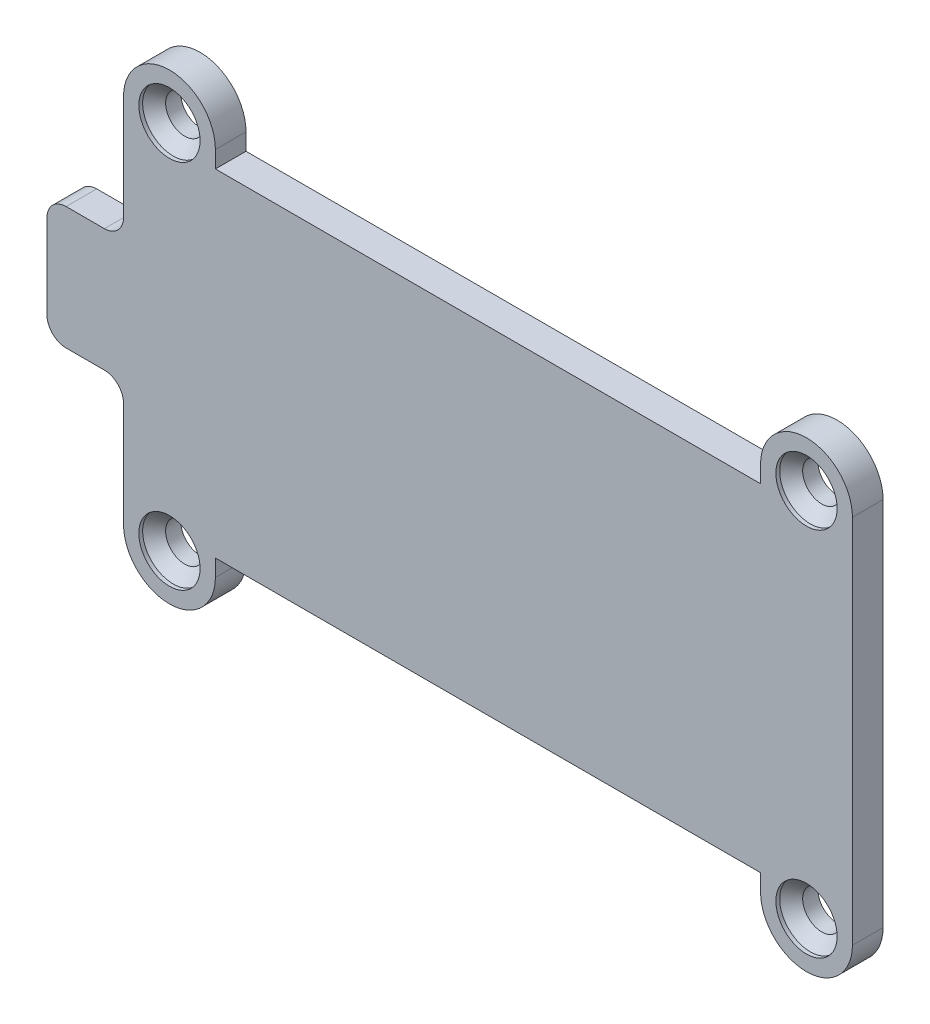
SolidWorks part; units mm, degrees
ref_plane "Front Plane" through (0, 0, 0) normal (0, 0, 1) x (1, 0, 0)
ref_plane "Top Plane" through (0, 0, 0) normal (0, 1, 0) x (1, 0, 0)
ref_plane "Right Plane" through (0, 0, 0) normal (1, 0, 0) x (0, 0, -1)
sketch "Sketch1" plane through (0, 0, 0) normal (0, 0, 1) x (1, 0, 0)
  line L3 (-28.8, 2.25) -> (-28.8, -2.25)
  line L4 (23.8, 12.1) -> (23.8, -12.1)
  line L52 (-25.05, 4) -> (-27.55, 4)
  line L53 (-28.8, 2.75) -> (-28.8, 2.25)
  line L54 (-28.8, 2.25) -> (-21.9, 2.25)
  line L55 (-21.9, 2.25) -> (-21.9, 9.1)
  line L56 (-21.9, 9.1) -> (21.9, 9.1)
  line L57 (21.9, 9.1) -> (21.9, 3.8)
  line L58 (21.9, 3.8) -> (23.8, 3.8)
  line L59 (23.8, 3.8) -> (23.8, 12.1)
  line L60 (17.8, 12.1) -> (17.8, 11)
  line L61 (17.8, 11) -> (-17.8, 11)
  line L62 (-17.8, 11) -> (-17.8, 12.1)
  line L63 (-23.8, 12.1) -> (-23.8, 5.25)
  line L64 (-25.05, 4) -> (-27.55, 4)
  line L65 (-28.8, 2.75) -> (-28.8, 2.25)
  line L72 (17.8, 12.1) -> (17.8, 11)
  line L73 (17.8, 11) -> (-17.8, 11)
  line L74 (-17.8, 11) -> (-17.8, 12.1)
  line L75 (-23.8, 12.1) -> (-23.8, 5.25)
  line L76 (-28.8, -2.25) -> (-28.8, -2.75)
  line L77 (-27.55, -4) -> (-25.05, -4)
  line L78 (-23.8, -5.25) -> (-23.8, -12.1)
  line L79 (-17.8, -12.1) -> (-17.8, -11)
  line L80 (-17.8, -11) -> (17.8, -11)
  line L81 (17.8, -11) -> (17.8, -12.1)
  line L82 (23.8, -12.1) -> (23.8, -3.8)
  line L83 (23.8, -3.8) -> (21.9, -3.8)
  line L84 (21.9, -3.8) -> (21.9, -9.1)
  line L85 (21.9, -9.1) -> (-21.9, -9.1)
  line L86 (-21.9, -9.1) -> (-21.9, -2.25)
  line L87 (-21.9, -2.25) -> (-28.8, -2.25)
  line L88 (-28.8, -2.25) -> (-28.8, -2.75)
  line L89 (-27.55, -4) -> (-25.05, -4)
  line L90 (-23.8, -5.25) -> (-23.8, -12.1)
  line L91 (-17.8, -12.1) -> (-17.8, -11)
  line L92 (-17.8, -11) -> (17.8, -11)
  line L93 (17.8, -11) -> (17.8, -12.1)
  circle A20 centre (-20.8, 12.1) radius 1.25
  circle A21 centre (20.8, 12.1) radius 1.25
  circle A22 centre (20.8, -12.1) radius 1.25
  circle A23 centre (-20.8, -12.1) radius 1.25
  arc A24 (-27.55, 4) -> (-28.8, 2.75) centre (-27.55, 2.75) ccw
  arc A25 (23.8, 12.1) -> (17.8, 12.1) centre (20.8, 12.1) ccw
  arc A26 (-17.8, 12.1) -> (-23.8, 12.1) centre (-20.8, 12.1) ccw
  arc A27 (-25.05, 4) -> (-23.8, 5.25) centre (-25.05, 5.25) ccw
  arc A28 (-27.55, 4) -> (-28.8, 2.75) centre (-27.55, 2.75) ccw
  arc A29 (23.8, 12.1) -> (17.8, 12.1) centre (20.8, 12.1) ccw
  arc A30 (-17.8, 12.1) -> (-23.8, 12.1) centre (-20.8, 12.1) ccw
  arc A31 (-25.05, 4) -> (-23.8, 5.25) centre (-25.05, 5.25) ccw
  arc A32 (-28.8, -2.75) -> (-27.55, -4) centre (-27.55, -2.75) ccw
  arc A33 (-23.8, -5.25) -> (-25.05, -4) centre (-25.05, -5.25) ccw
  arc A34 (-23.8, -12.1) -> (-17.8, -12.1) centre (-20.8, -12.1) ccw
  arc A35 (17.8, -12.1) -> (23.8, -12.1) centre (20.8, -12.1) ccw
  arc A36 (-28.8, -2.75) -> (-27.55, -4) centre (-27.55, -2.75) ccw
  arc A37 (-23.8, -5.25) -> (-25.05, -4) centre (-25.05, -5.25) ccw
  arc A38 (-23.8, -12.1) -> (-17.8, -12.1) centre (-20.8, -12.1) ccw
  arc A39 (17.8, -12.1) -> (23.8, -12.1) centre (20.8, -12.1) ccw
  dimension "D1" = 0
  dimension "D3" = 2.5
  dimension "D2" = 0
extrude "Boss-Extrude1" add sketch "Sketch1" along normal blind 2
hole_wizard "CSK for M2 Flat Head Machine Screw1" positions "Sketch2" profile "Sketch3" countersink size "M2" standard "ANSI Metric"
sketch "Sketch2" plane through (0, 0, 2) normal (0, 0, 1) x (1, 0, 0)
  point P0 (-20.8, 12.1)
  point P3 (20.8, 12.1)
  point P6 (20.8, -12.1)
  point P9 (-20.8, -12.1)
sketch "Sketch3" plane through (-20.8, 12.1, 2) normal (1, 0, 0) x (0, -1, 0)
  line L0 (0, 0) -> (0, 4.4009)
  line L1 (0, 4.4009) -> (1, 3.8)
  line L2 (1, 3.8) -> (1, 1.25)
  line L3 (1, 1.25) -> (2, 0.25)
  line L4 (2, 0.25) -> (2, 0)
  line L6 (2, 0) -> (0, 0)
  line L7 (-1, 1.25) -> (-2, 0.25) construction
  line L10 (0, 4.4009) -> (-1, 3.8) construction
  line L11 (0, -6.35) -> (0, 107.95) construction
  dimension "Hole Dia." = 2
  dimension "Hole Depth" = 3.8
  dimension "C'Sink Dia." = 4
  dimension "C'Sink Angle" = 90
  dimension "Drill Angle" = 118
  dimension "Head Clearance" = 0.25
